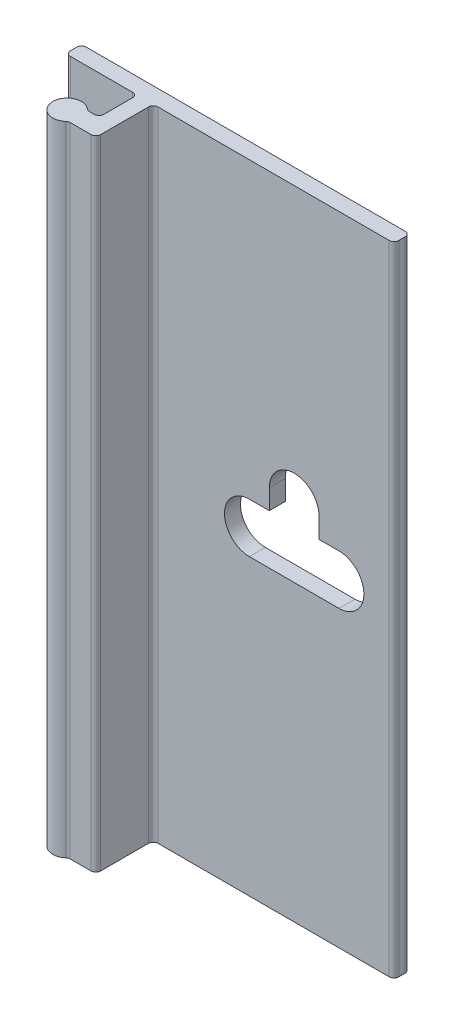
SolidWorks part; units mm, degrees
ref_plane "Front Plane" through (0, 0, 0) normal (0, 0, 1) x (1, 0, 0)
ref_plane "Top Plane" through (0, 0, 0) normal (0, 1, 0) x (1, 0, 0)
ref_plane "Right Plane" through (0, 0, 0) normal (1, 0, 0) x (0, 0, -1)
sketch "Sketch2" plane through (0, 0, 0) normal (0, 1, 0) x (1, 0, 0)
  line L0 (0, 7.209) -> (0, -15.6826) construction
  line L16 (-5.969, 0) -> (19.431, 0)
  line L18 (19.812, -0.381) -> (19.812, -0.889)
  line L19 (19.431, -1.27) -> (1.016, -1.27)
  line L20 (0.635, -1.651) -> (0.635, -3.937)
  line L52 (-0.635, -1.651) -> (-0.635, -3.937)
  line L53 (-8.0148, -5.08) -> (8.0148, -5.08) construction
  line L54 (-1.405, -4.318) -> (-1.016, -4.318)
  line L55 (-1.405, -5.842) -> (1.405, -5.842)
  line L56 (1.016, -4.318) -> (1.405, -4.318)
  line L57 (-1.016, -1.27) -> (-5.969, -1.27)
  line L58 (-6.35, -0.889) -> (-6.35, -0.381)
  arc A11 (19.431, 0) -> (19.812, -0.381) centre (19.431, -0.381) cw
  arc A12 (19.812, -0.889) -> (19.431, -1.27) centre (19.431, -0.889) cw
  arc A19 (1.016, -1.27) -> (0.635, -1.651) centre (1.016, -1.651) ccw
  arc A20 (-1.657, -4.2227) -> (-1.657, -5.9373) centre (-2.413, -5.08) ccw
  arc A21 (1.657, -5.9373) -> (1.657, -4.2227) centre (2.413, -5.08) ccw
  arc A22 (0.635, -3.937) -> (1.016, -4.318) centre (1.016, -3.937) ccw
  arc A23 (-0.635, -3.937) -> (-1.016, -4.318) centre (-1.016, -3.937) cw
  arc A24 (1.405, -5.842) -> (1.657, -5.9373) centre (1.405, -6.223) cw
  arc A25 (1.657, -4.2227) -> (1.405, -4.318) centre (1.405, -3.937) cw
  arc A26 (-1.405, -5.842) -> (-1.657, -5.9373) centre (-1.405, -6.223) ccw
  arc A27 (-1.405, -4.318) -> (-1.657, -4.2227) centre (-1.405, -3.937) cw
  arc A28 (-6.35, -0.381) -> (-5.969, 0) centre (-5.969, -0.381) cw
  arc A29 (-5.969, -1.27) -> (-6.35, -0.889) centre (-5.969, -0.889) cw
  arc A30 (-1.016, -1.27) -> (-0.635, -1.651) centre (-1.016, -1.651) cw
  point P7 (0, -5.08)
  point P16 (19.812, 0)
  point P19 (19.812, -1.27)
  point P22 (0.635, -1.27)
  point P30 (0.635, -4.318)
  point P36 (1.5611, -5.842)
  point P39 (1.5611, -4.318)
  point P42 (-1.5611, -5.842)
  point P45 (-1.5611, -4.318)
  dimension "D7" = 0.381
  dimension "D6" = 2.286
  dimension "D10" = 1.524
  dimension "D11" = 19.812
  dimension "D12" = 6.35
  dimension "D2" = 1.27
  dimension "D3" = 1.27
  dimension "D4" = 0.635
  dimension "D5" = 5.08
  dimension "D8" = 2.413
  dimension "D9" = 2.413
extrude "Boss-Extrude1" add sketch "Sketch2" along normal blind 50.8
sketch "Sketch4" plane through (0, 0, 0) normal (0, -1, 0) x (1, 0, 0)
  line L1 (0.635, 1.651) -> (3.556, 1.651)
  line L2 (0.635, 1.651) -> (0.635, 6.223)
  line L3 (0.635, 6.223) -> (3.556, 6.223)
  line L4 (3.556, 1.651) -> (3.556, 6.223)
  arc A0 (1.657, 4.2227) -> (1.657, 5.9373) centre (2.413, 5.08) ccw construction
extrude "Cut-Extrude2" cut sketch "Sketch4" against normal through all
fillet "Fillet1" radius 0.381 1 edges at (0.635, 25.4, 5.842)
sketch "Sketch3" plane through (0, 0, 1.27) normal (0, 0, 1) x (1, 0, 0)
  line L0 (8.2931, 25.4) -> (15.4305, 25.4) construction
  line L1 (8.2931, 27.3812) -> (9.8806, 27.3812)
  line L2 (8.2931, 23.4188) -> (15.4305, 23.4188)
  line L3 (19.812, 50.8) -> (19.812, 0) construction
  line L4 (13.843, 28.9814) -> (13.843, 27.3812)
  line L5 (9.8806, 28.9814) -> (9.8806, 27.3812)
  line L6 (13.843, 27.3812) -> (15.4305, 27.3812)
  line L7 (1.016, 0) -> (19.431, 0) construction
  arc A0 (8.2931, 27.3812) -> (8.2931, 23.4188) centre (8.2931, 25.4) ccw
  arc A1 (15.4305, 23.4188) -> (15.4305, 27.3812) centre (15.4305, 25.4) ccw
  arc A2 (13.843, 28.9814) -> (9.8806, 28.9814) centre (11.8618, 28.9814) ccw
  point P2 (11.8618, 25.4)
  dimension "D2" = 1.9812
  dimension "D3" = 3.5814
  dimension "D1" = 7.1374
  dimension "D4" = 7.9502
  dimension "D5" = 25.4
extrude "Cut-Extrude1" cut sketch "Sketch3" against normal through all
pattern_linear "LPattern1" [suppressed] count 2 spacing 203.2
